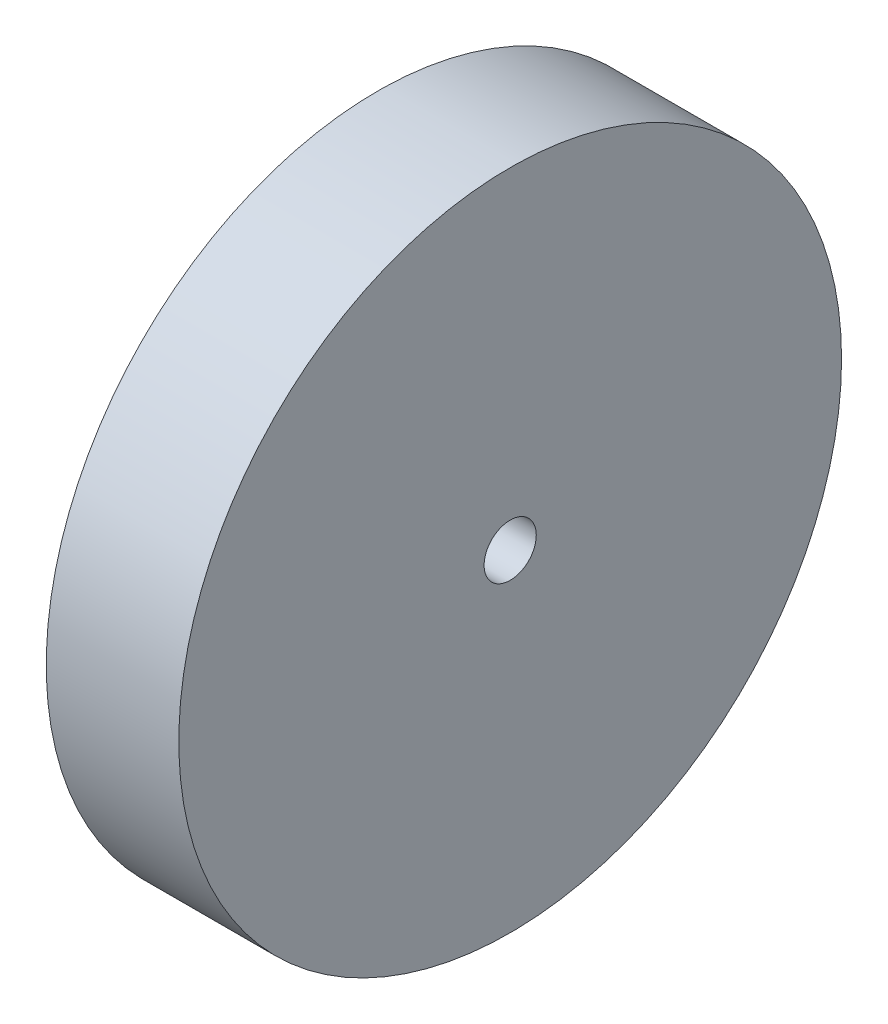
SolidWorks part; units mm, degrees
ref_plane "Front Plane" through (0, 0, 0) normal (0, 0, 1) x (1, 0, 0)
ref_plane "Top Plane" through (0, 0, 0) normal (0, 1, 0) x (1, 0, 0)
ref_plane "Right Plane" through (0, 0, 0) normal (1, 0, 0) x (0, 0, -1)
sketch "Sketch1" plane through (0, 0, 0) normal (1, 0, 0) x (0, 0, -1)
  circle A0 centre (0, 0) radius 31.75
  circle A1 centre (0, 0) radius 2.5
  dimension "D1" = 5
  dimension "D2" = 63.5
extrude "Boss-Extrude1" add sketch "Sketch1" along normal blind 12.7
